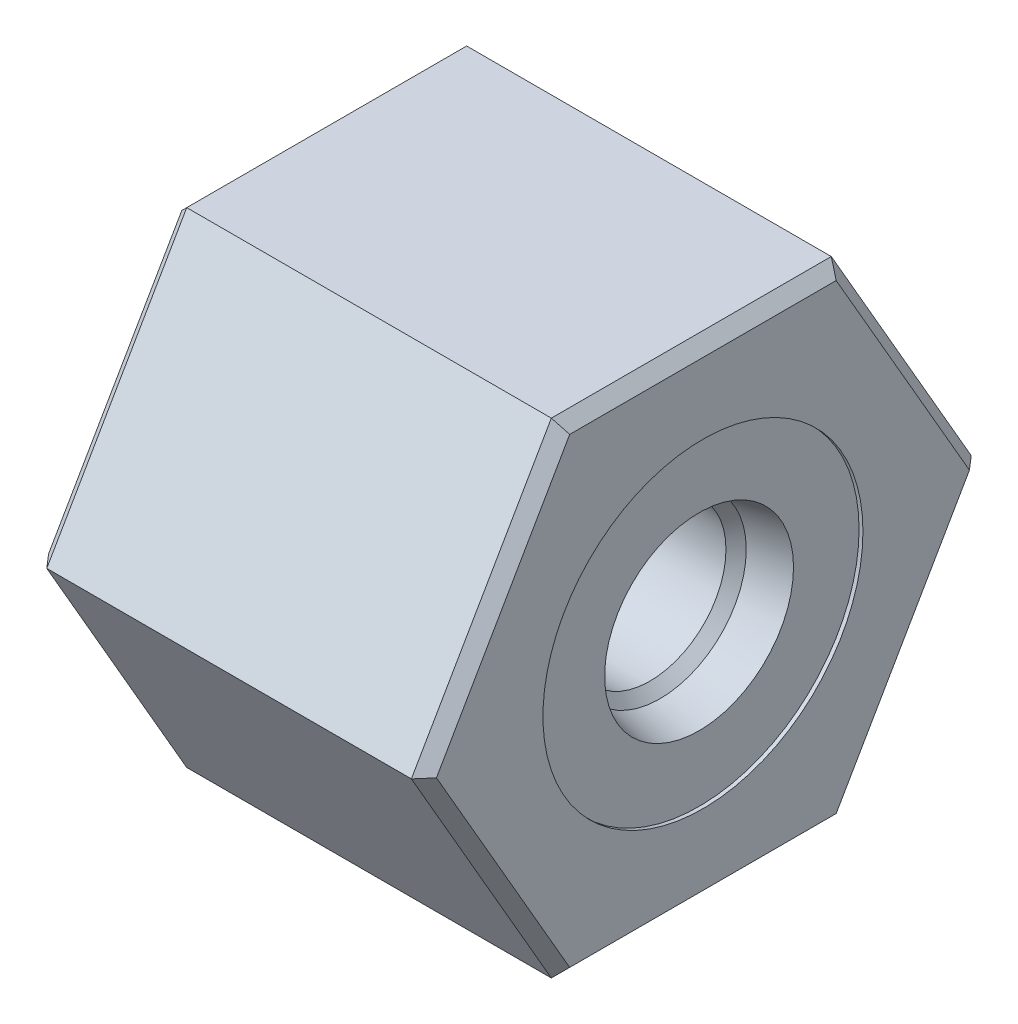
SolidWorks part; units mm, degrees
material "Alloy Steel"
ref_plane "Front Plane" through (0, 0, 0) normal (0, 0, 1) x (1, 0, 0)
ref_plane "Top Plane" through (0, 0, 0) normal (0, 1, 0) x (1, 0, 0)
ref_plane "Right Plane" through (0, 0, 0) normal (1, 0, 0) x (0, 0, -1)
ref_plane "Plane1" through (0, 0, 0) normal (-1, 0, 0) x (0, -1, 0)
sketch "Sketch1" plane through (0, 0, 0) normal (-1, 0, 0) x (0, -1, 0)
  line L0 (15.875, 9.1654) -> (0, 18.3309)
  line L1 (0, 18.3309) -> (-15.875, 9.1654)
  line L2 (-15.875, 9.1654) -> (-15.875, -9.1654)
  line L3 (-15.875, -9.1654) -> (0, -18.3309)
  line L4 (0, -18.3309) -> (15.875, -9.1654)
  line L5 (15.875, -9.1654) -> (15.875, 9.1654)
extrude "Extrude1" add sketch "Sketch1" against normal blind 25.4
sketch "Sketch2" plane through (0, 0, 0) normal (0, 0, 1) x (1, 0, 0)
  line L0 (0, 11.8872) -> (0, 0)
  line L1 (0, 0) -> (25.4, 0)
  line L2 (25.4, 0) -> (25.4, 10.4775)
  line L3 (25.4, 10.4775) -> (25.146, 10.4775)
  line L4 (25.146, 10.4775) -> (25.146, 6.1849)
  line L5 (25.146, 6.1849) -> (22.5933, 5.6423)
  line L6 (22.5933, 5.6423) -> (21.9294, 4.9784)
  line L7 (21.9294, 4.9784) -> (13.462, 4.9784)
  line L8 (13.462, 4.9784) -> (13.462, 11.7221)
  line L9 (13.462, 11.7221) -> (10.16, 11.7221)
  line L10 (9.7852, 11.8872) -> (0, 11.8872)
  line L11 (0, 0) -> (25.4, 0) construction
  arc A0 (10.16, 11.7221) -> (9.7852, 11.8872) centre (9.7852, 11.3792) ccw
revolve "Cut-Revolve1" cut sketch "Sketch2" angle 360 about L11
chamfer "Chamfer1" distance 0.254 angle 45 1 edges at (0, 0, -11.8872)
chamfer "Chamfer2" distance 0.762 angle 45 1 edges at (13.462, 0, -4.9784)
chamfer "Chamfer3" distance 0.762 angle 45 6 edges at (0, 7.9375, -13.7482) (0, -7.9375, -13.7482) (0, 15.875, 0) (0, -15.875, 0) (0, 7.9375, 13.7482) (0, -7.9375, 13.7482)
chamfer "Chamfer4" distance 0.762 angle 45 6 edges at (25.4, 7.9375, -13.7482) (25.4, 15.875, 0) (25.4, -7.9375, -13.7482) (25.4, 7.9375, 13.7482) (25.4, -15.875, 0) (25.4, -7.9375, 13.7482)
